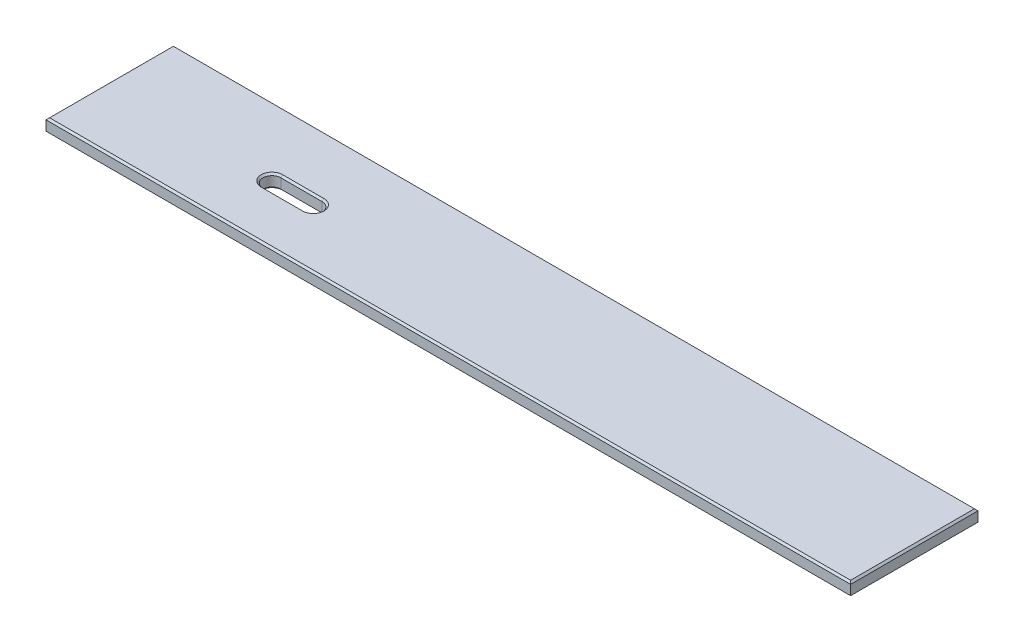
SolidWorks part; units mm, degrees
material "Oak"
ref_plane "Front Plane" through (0, 0, 0) normal (0, 0, 1) x (1, 0, 0)
ref_plane "Top Plane" through (0, 0, 0) normal (0, 1, 0) x (1, 0, 0)
ref_plane "Right Plane" through (0, 0, 0) normal (1, 0, 0) x (0, 0, -1)
sketch "Sketch1" plane through (0, 0, 0) normal (0, 1, 0) x (1, 0, 0)
  line L1 (0, 0) -> (1143, 0)
  line L2 (0, 0) -> (0, 180.975)
  line L3 (0, 180.975) -> (1143, 180.975)
  line L4 (1143, 0) -> (1143, 180.975)
  line L6 (238.125, 95.4913) -> (296.8752, 95.4913)
  line L8 (238.125, 70.0913) -> (296.8752, 70.0913)
  arc A4 (296.8752, 70.0913) -> (296.8752, 95.4913) centre (296.8752, 82.7913) ccw
  arc A5 (238.125, 95.4913) -> (238.125, 70.0913) centre (238.125, 82.7913) ccw
  point P14 (296.8752, 95.4913)
  dimension "D7" = 25.4
  dimension "D1" = 180.975
  dimension "D2" = 1143
  dimension "D3" = 58.7502
  dimension "D4" = 82.7913
  dimension "D5" = 238.125
extrude "Boss-Extrude1" add sketch "Sketch1" along normal blind 19.05
chamfer "Chamfer1" distance 2.54 angle 45 8 edges at (571.5, 19.05, -180.975) (1143, 19.05, -90.4875) (571.5, 19.05, 0) (0, 19.05, -90.4875) (267.5001, 19.05, -95.4913) (267.5001, 19.05, -70.0913) (225.425, 19.05, -82.7913) (309.5752, 19.05, -82.7913)
chamfer "Chamfer2" distance 2.54 angle 45 8 edges at (267.5001, 0, -95.4913) (267.5001, 0, -70.0913) (571.5, 0, 0) (1143, 0, -90.4875) (571.5, 0, -180.975) (0, 0, -90.4875) (225.425, 0, -82.7913) (309.5752, 0, -82.7913)
